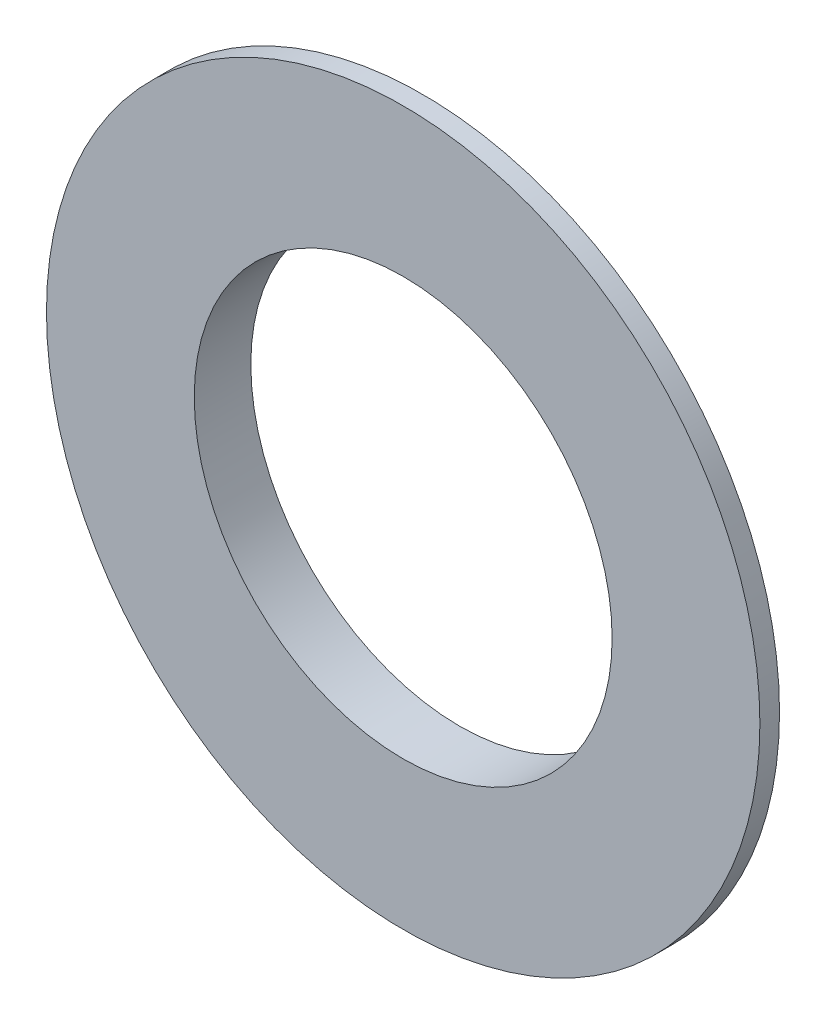
SolidWorks part; units mm, degrees
ref_plane "Front Plane" through (0, 0, 0) normal (0, 0, 1) x (1, 0, 0)
ref_plane "Top Plane" through (0, 0, 0) normal (0, 1, 0) x (1, 0, 0)
ref_plane "Right Plane" through (0, 0, 0) normal (1, 0, 0) x (0, 0, -1)
sketch "Sketch1" plane through (0, 0, 0) normal (0, 1, 0) x (1, 0, 0)
  line L0 (0, 0) -> (-28.8163, 0) construction
  line L1 (-18.9167, 0) -> (-18.9167, 1.0408)
  line L2 (-18.9167, 1.0408) -> (-11.08, 3)
  line L3 (-11.08, 3) -> (-11.08, 0)
  line L4 (-11.08, 0) -> (-18.9167, 0)
  line L5 (0, 0) -> (0, 8.353) construction
  dimension "D1" = 3
  dimension "D2" = 11.08
revolve "Revolve1" add sketch "Sketch1" angle 360 about L5
